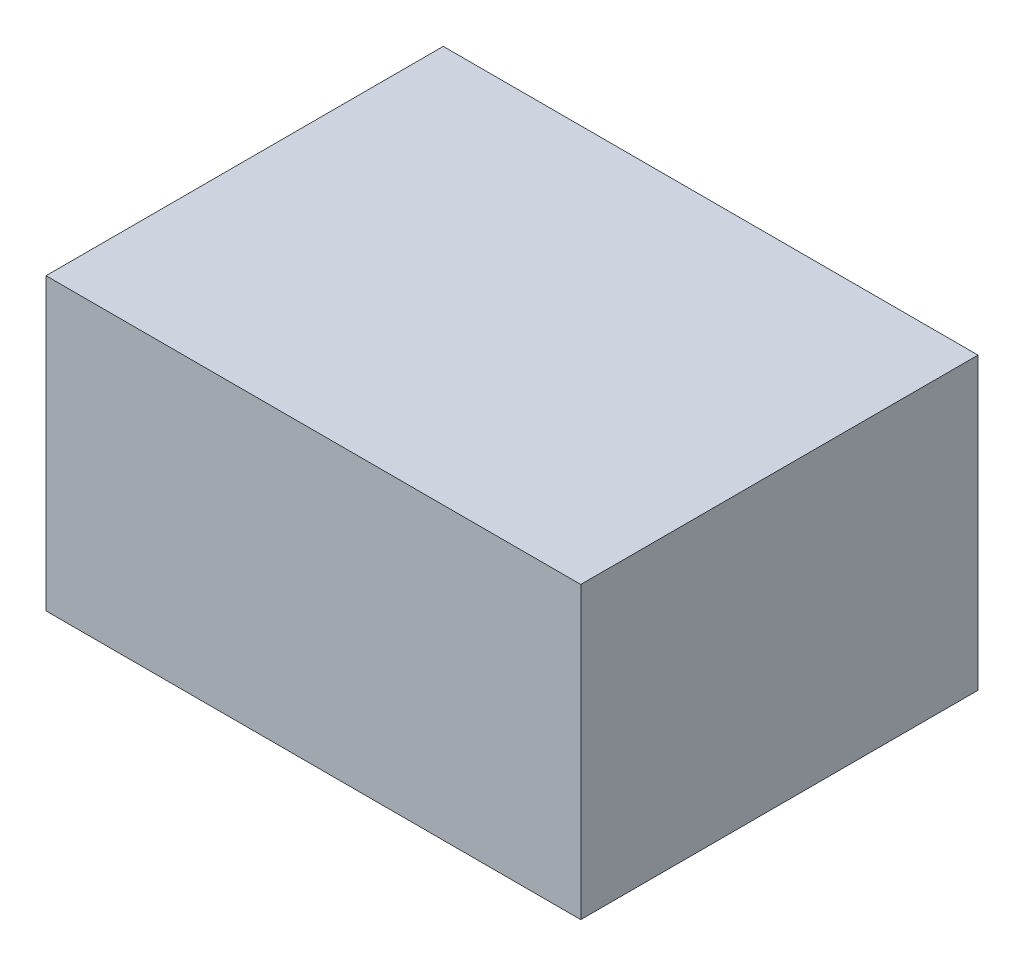
SolidWorks part; units mm, degrees
ref_plane "Płaszczyzna przednia" through (0, 0, 0) normal (0, 0, 1) x (1, 0, 0)
ref_plane "Płaszczyzna górna" through (0, 0, 0) normal (0, 1, 0) x (1, 0, 0)
ref_plane "Płaszczyzna prawa" through (0, 0, 0) normal (1, 0, 0) x (0, 0, -1)
ref_plane "Plane1" through (0, -0.475, 0) normal (0, -1, 0) x (1, 0, 0)
sketch "Sketch1" plane through (0, -0.475, 0) normal (0, -1, 0) x (1, 0, 0)
  line L0 (-0.875, 0) -> (0.875, 0)
  line L1 (0.875, 0) -> (0.875, 1.3)
  line L2 (0.875, 1.3) -> (-0.875, 1.3)
  line L3 (-0.875, 1.3) -> (-0.875, 0)
extrude "Boss-Extrude1" add sketch "Sketch1" against normal blind 0.95
